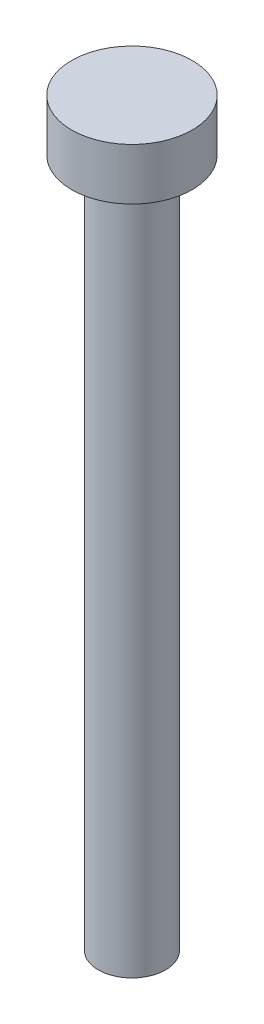
SolidWorks part; units mm, degrees
ref_plane "Front Plane" through (0, 0, 0) normal (0, 0, 1) x (1, 0, 0)
ref_plane "Top Plane" through (0, 0, 0) normal (0, 1, 0) x (1, 0, 0)
ref_plane "Right Plane" through (0, 0, 0) normal (1, 0, 0) x (0, 0, -1)
sketch "Sketch1" plane through (0, 0, 0) normal (0, 1, 0) x (1, 0, 0)
  circle A0 centre (0, 0) radius 3.5
  dimension "D1" = 7
extrude "Boss-Extrude1" add sketch "Sketch1" along normal blind 3
sketch "Sketch2" plane through (0, 0, 0) normal (0, -1, 0) x (1, 0, 0)
  circle A0 centre (0, 0) radius 1.95
  dimension "D1" = 3.9
extrude "Boss-Extrude2" add sketch "Sketch2" along normal blind 40
